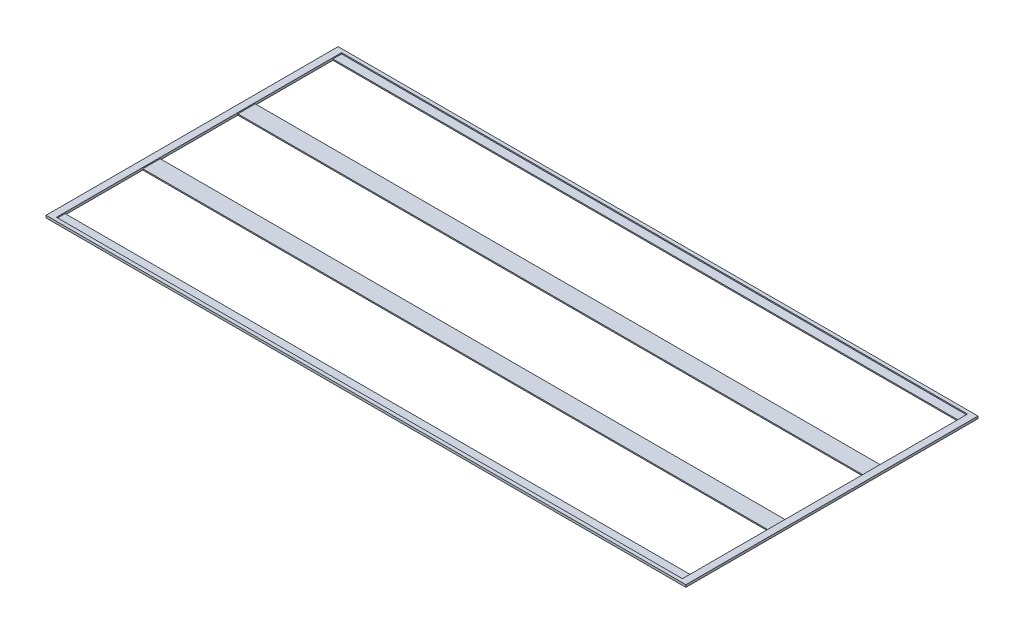
SolidWorks part; units mm, degrees
material "PVC Rigid"
ref_plane "Front Plane" through (0, 0, 0) normal (0, 0, 1) x (1, 0, 0)
ref_plane "Top Plane" through (0, 0, 0) normal (0, 1, 0) x (1, 0, 0)
ref_plane "Right Plane" through (0, 0, 0) normal (1, 0, 0) x (0, 0, -1)
sketch "Sketch1" plane through (0, 0, 0) normal (0, 1, 0) x (1, 0, 0)
  line L1 (-540, -246) -> (540, -246)
  line L2 (-540, -246) -> (-540, 246)
  line L3 (-540, 246) -> (540, 246)
  line L4 (540, -246) -> (540, 246)
  line L5 (-540, -246) -> (540, 246) construction
  line L6 (-540, 246) -> (540, -246) construction
  point P0 (0, 0)
extrude "Boss-Extrude1" add sketch "Sketch1" along normal blind 2 contours L3 L4 L1 L2
sketch "Sketch4" plane through (0, 0, 0) normal (0, 1, 0) x (1, 0, 0)
  line L1 (-552, -252.006) -> (552, -252.006)
  line L2 (-552, -252.006) -> (-552, 252.006)
  line L3 (-552, 252.006) -> (552, 252.006)
  line L4 (552, -252.006) -> (552, 252.006)
  line L5 (-552, -252.006) -> (552, 252.006) construction
  line L6 (-552, 252.006) -> (552, -252.006) construction
  line L7 (-540, -246) -> (540, -246)
  line L8 (-540, -246) -> (-540, 246)
  line L9 (-540, 246) -> (540, 246)
  line L10 (540, -246) -> (540, 246)
  line L11 (-540, -246) -> (540, 246) construction
  line L12 (-540, 246) -> (540, -246) construction
  point P0 (0, 0)
  point P6 (0, 0)
extrude "Boss-Extrude3" add sketch "Sketch4" along normal blind 4 contours L8 L9 L10 L7 | L2 L3 L4 L1
sketch "Sketch5" plane through (0, 2, 0) normal (0, 1, 0) x (1, 0, 0)
  line L0 (-540, 246) -> (-540, 231) construction
  line L1 (-540, -246) -> (-540, 246) construction
  line L2 (-540, 231) -> (-540, 97)
  line L3 (-540, 231) -> (540, 231)
  line L4 (540, -246) -> (540, 246) construction
  line L5 (540, 231) -> (540, 97)
  line L6 (540, 97) -> (-540, 97)
extrude "Cut-Extrude2" cut sketch "Sketch5" against normal blind 4
pattern_linear "LPattern2" count 3 spacing 164 along (0, 0, 1) of "Cut-Extrude2"
